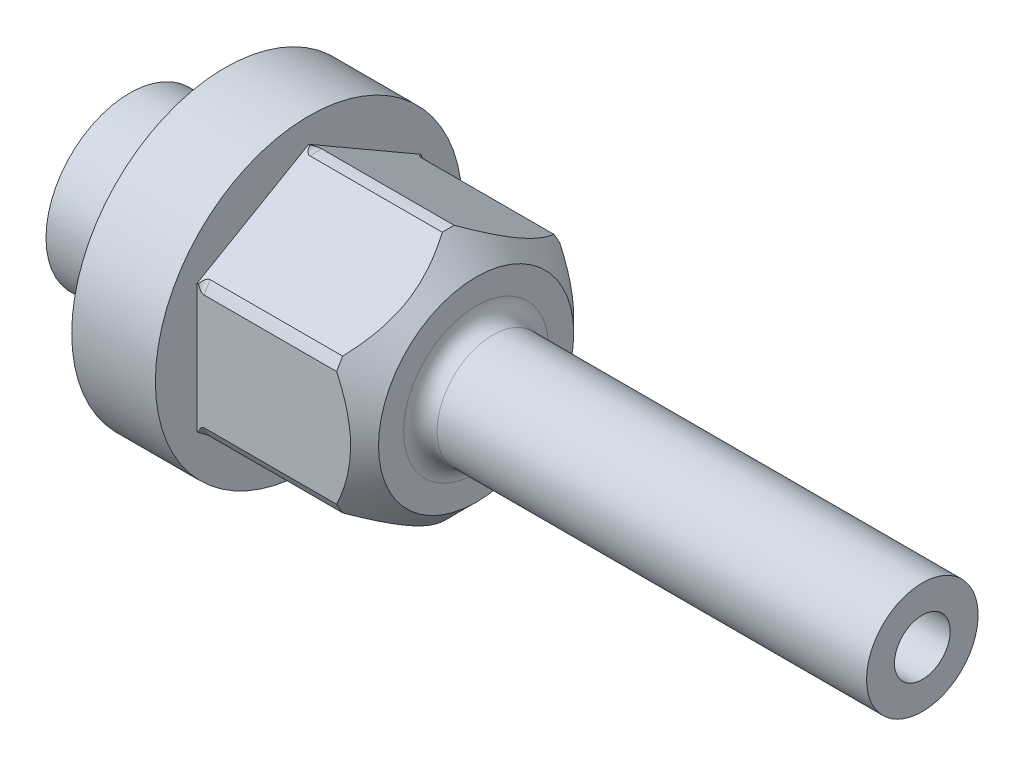
SolidWorks part; units mm, degrees
material "1.4404 (X2CrNiMo17-12-2)"
ref_plane "Front Plane" through (0, 0, 0) normal (0, 0, 1) x (1, 0, 0)
ref_plane "Top Plane" through (0, 0, 0) normal (0, 1, 0) x (1, 0, 0)
ref_plane "Right Plane" through (0, 0, 0) normal (1, 0, 0) x (0, 0, -1)
ref_axis "Axis1" through (-88.99, 0, 0) along (1, 0, 0)
sketch "Sketch1" plane through (0, 0, 0) normal (0, 0, 1) x (1, 0, 0)
  line L0 (0, 5.5) -> (0, 4.75)
  line L1 (1.15, 3) -> (-3.4226, 3)
  line L2 (-3.4226, 3) -> (-4, 2)
  line L3 (-4, 2) -> (-4, 1)
  line L4 (-4, 1) -> (25, 1)
  line L5 (25, 1) -> (25, 2)
  line L6 (25, 2) -> (9.6, 2)
  line L7 (9, 2.6) -> (9, 3.5)
  line L8 (8, 4.5) -> (3.25, 4.5)
  line L9 (3, 4.75) -> (3, 5.5)
  line L10 (3, 5.5) -> (0, 5.5)
  line L11 (-88.99, 0) -> (88.99, 0) construction
  line L12 (9, 3.5) -> (8, 4.5)
  line L13 (0.25, 4.5) -> (1.15, 4.5)
  line L14 (1.4, 4.25) -> (1.4, 3.25)
  line L15 (0, 4.75) -> (0.25, 4.5)
  arc A0 (9.6, 2) -> (9, 2.6) centre (9.6, 2.6) cw
  arc A2 (1.15, 4.5) -> (1.4, 4.25) centre (1.15, 4.25) cw
  arc A3 (1.15, 3) -> (1.4, 3.25) centre (1.15, 3.25) ccw
  arc A4 (3.25, 4.5) -> (3, 4.75) centre (3.25, 4.75) cw
  point P9 (9, 4.5)
  point P16 (0, 4.5)
  dimension "D8" = 0.6
  dimension "D15" = 0.25
  dimension "D17" = 0.25
  dimension "D1" = 2
  dimension "D2" = 4
  dimension "D3" = 4
  dimension "D4" = 30
  dimension "D5" = 3
  dimension "D6" = 6
  dimension "D7" = 25
  dimension "D9" = 6
  dimension "D10" = 11
  dimension "D12" = 9
  dimension "D13" = 1
  dimension "D14" = 1.4
  dimension "D16" = 9
revolve "Revolve1" add sketch "Sketch1" angle 360 about axis through (-88.99, 0, 0) along (1, 0, 0)
sketch "Sketch2" plane through (0, 0, 0) normal (1, 0, 0) x (0, 0, -1)
  line L1 (0, 4.6188) -> (-4, 2.3094)
  line L2 (-4, 2.3094) -> (-4, -2.3094)
  line L3 (-4, -2.3094) -> (0, -4.6188)
  line L4 (0, -4.6188) -> (4, -2.3094)
  line L5 (4, -2.3094) -> (4, 2.3094)
  line L6 (4, 2.3094) -> (0, 4.6188)
  circle A0 centre (0, 0) radius 4 construction
  dimension "D1" = 8
extrude "Cut-Extrude1" cut sketch "Sketch2" along normal blind 10 from offset 3 flip side to cut
